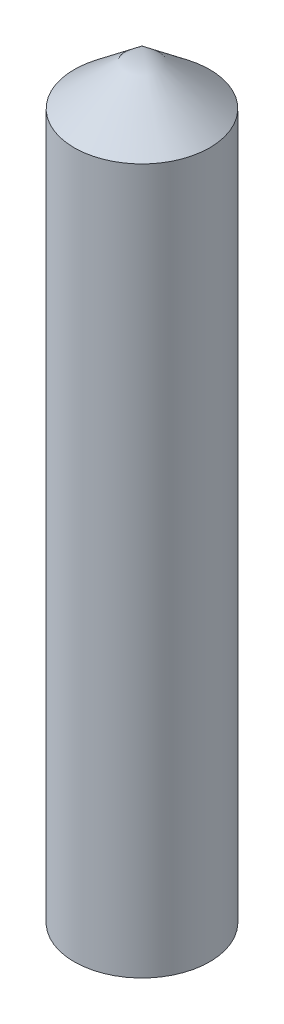
SolidWorks part; units mm, degrees
ref_plane "Face" through (0, 0, 0) normal (0, 0, 1) x (1, 0, 0)
ref_plane "Dessus" through (0, 0, 0) normal (0, 1, 0) x (1, 0, 0)
ref_plane "Droite" through (0, 0, 0) normal (1, 0, 0) x (0, 0, -1)
sketch "Esquisse1" plane through (0, 0, 0) normal (0, 1, 0) x (1, 0, 0)
  circle A0 centre (0, 0) radius 12.5
  dimension "D1" = 25
extrude "Boss.-Extru.1" add sketch "Esquisse1" along normal blind 130
sketch "Esquisse2" plane through (0, 0, 0) normal (0, 0, 1) x (1, 0, 0)
  line L0 (-12.5, 130) -> (0, 140)
  line L1 (0, 140) -> (0, 130)
  line L2 (12.5, 130) -> (-12.5, 130) construction
  line L3 (0, 130) -> (-12.5, 130)
  dimension "D1" = 10
revolve "Révolution1" add sketch "Esquisse2" angle 360 about L1
